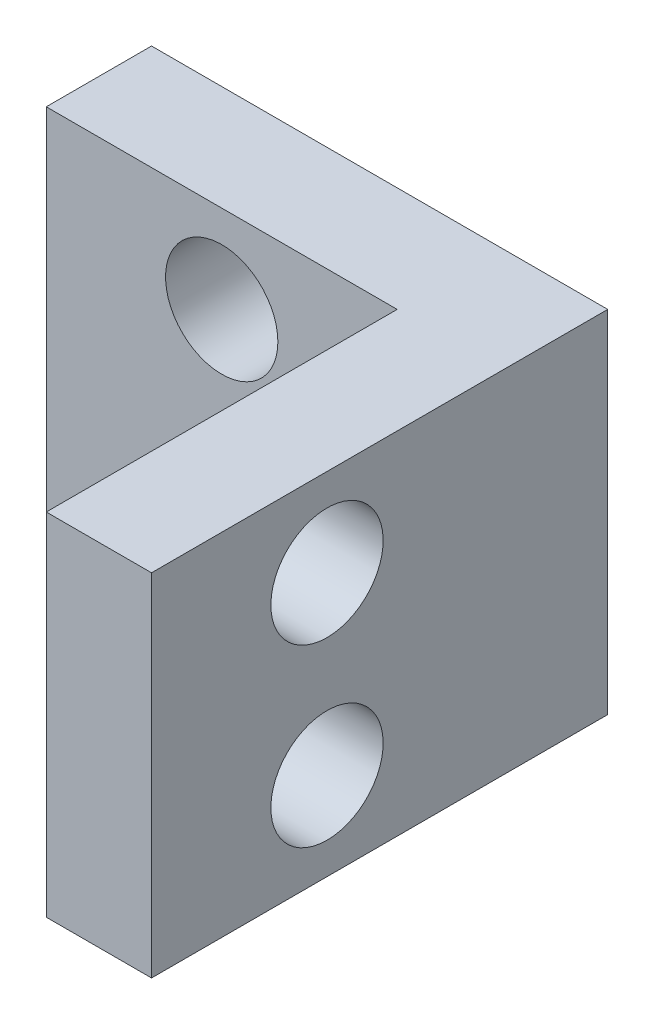
SolidWorks part; units mm, degrees
ref_plane "Front Plane" through (0, 0, 0) normal (0, 0, 1) x (1, 0, 0)
ref_plane "Top Plane" through (0, 0, 0) normal (0, 1, 0) x (1, 0, 0)
ref_plane "Right Plane" through (0, 0, 0) normal (1, 0, 0) x (0, 0, -1)
sketch "Sketch1" plane through (0, 0, 0) normal (0, 0, 1) x (1, 0, 0)
  line L1 (0, 0) -> (10, 0)
  line L2 (0, 0) -> (0, -10)
  line L3 (0, -10) -> (10, -10)
  line L4 (10, 0) -> (10, -10)
  dimension "D1" = 10
  dimension "D2" = 10
extrude "Boss-Extrude1" add sketch "Sketch1" along normal blind 3
sketch "Sketch2" plane through (10, 0, 0) normal (1, 0, 0) x (0, 0, -1)
  line L1 (0, 0) -> (-13, 0)
  line L2 (0, 0) -> (0, -10)
  line L3 (0, -10) -> (-13, -10)
  line L4 (-13, 0) -> (-13, -10)
  dimension "D1" = 13
  dimension "D2" = 10
extrude "Boss-Extrude2" add sketch "Sketch2" along normal blind 3
sketch "Sketch3" plane through (0, 0, 3) normal (0, 0, 1) x (1, 0, 0)
  line L0 (0, 0) -> (0, -10) construction
  line L1 (10, 0) -> (0, 0) construction
  line L2 (10, -10) -> (10, 0) construction
  circle A0 centre (5, -2.5) radius 1.6
  circle A1 centre (5, -7.5) radius 1.6
  dimension "D1" = 3.2
  dimension "D2" = 3.2
  dimension "D3" = 5
  dimension "D4" = 5
  dimension "D5" = 2.5
extrude "Cut-Extrude1" cut sketch "Sketch3" against normal through all
sketch "Sketch4" plane through (10, 0, 0) normal (-1, 0, 0) x (0, 0, 1)
  line L0 (3, 0) -> (13, 0) construction
  line L1 (13, 0) -> (13, -10) construction
  circle A0 centre (8, -2.5) radius 1.6
  circle A1 centre (8, -7.5) radius 1.6
  dimension "D1" = 3.2
  dimension "D2" = 3.2
  dimension "D3" = 2.5
  dimension "D5" = 5
  dimension "D6" = 5
  dimension "D4" = 5
extrude "Cut-Extrude2" cut sketch "Sketch4" against normal through all
